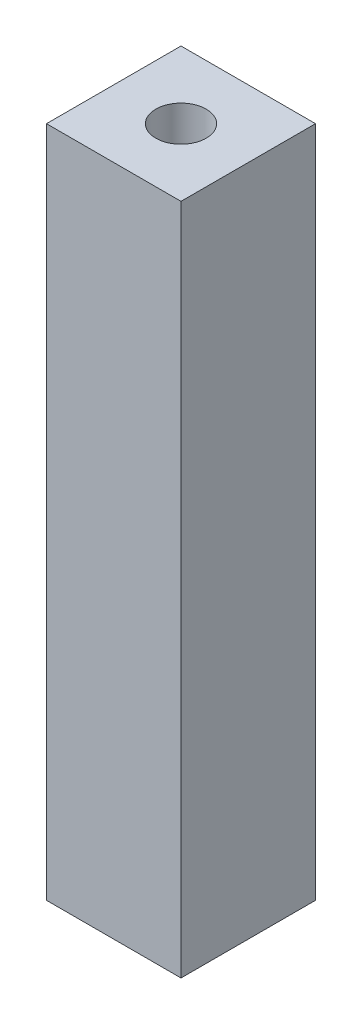
SolidWorks part; units mm, degrees
ref_plane "Front Plane" through (0, 0, 0) normal (0, 0, 1) x (1, 0, 0)
ref_plane "Top Plane" through (0, 0, 0) normal (0, 1, 0) x (1, 0, 0)
ref_plane "Right Plane" through (0, 0, 0) normal (1, 0, 0) x (0, 0, -1)
sketch "Sketch1" plane through (0, 0, 0) normal (0, 1, 0) x (1, 0, 0)
  line L1 (-4, -4) -> (4, -4)
  line L2 (-4, -4) -> (-4, 4)
  line L3 (-4, 4) -> (4, 4)
  line L4 (4, -4) -> (4, 4)
  line L5 (-4, -4) -> (4, 4) construction
  line L6 (-4, 4) -> (4, -4) construction
  point P0 (0, 0)
  dimension "D1" = 8
extrude "Boss-Extrude1" add sketch "Sketch1" along normal blind 40
sketch "Sketch2" plane through (0, 40, 0) normal (0, 1, 0) x (1, 0, 0)
  circle A0 centre (0, 0) radius 1.5
  dimension "D1" = 3
extrude "Cut-Extrude1" cut sketch "Sketch2" against normal through all
